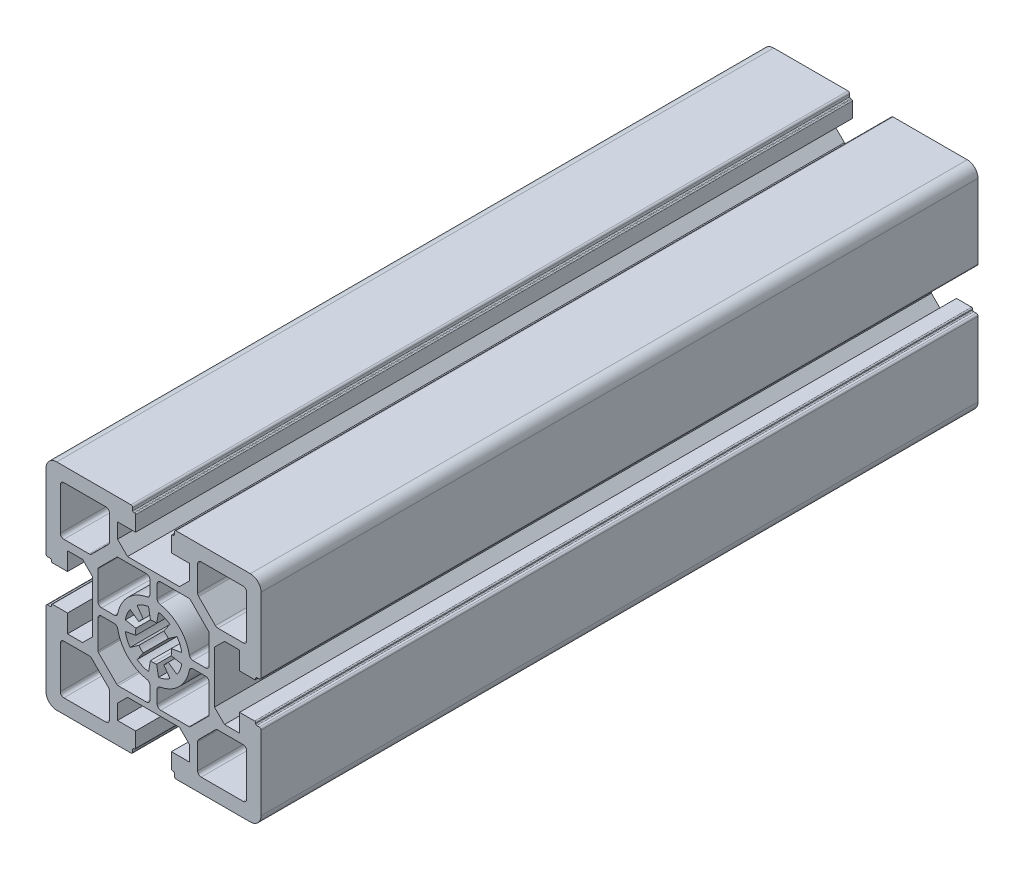
SolidWorks part; units mm, degrees
ref_plane "Front Plane" through (0, 0, 0) normal (0, 0, 1) x (1, 0, 0)
ref_plane "Top Plane" through (0, 0, 0) normal (0, 1, 0) x (1, 0, 0)
ref_plane "Right Plane" through (0, 0, 0) normal (1, 0, 0) x (0, 0, -1)
sketch "Sketch1" plane through (0, 0, 0) normal (0, 0, 1) x (1, 0, 0)
  line L0 (25, 12.3) -> (17.9642, 12.3)
  line L1 (17.2571, 12.5929) -> (12.5929, 17.2571)
  line L2 (12.3, 17.9642) -> (12.3, 25)
  line L3 (25, 26) -> (13.3, 26)
  line L4 (26, 13.3) -> (26, 25)
  line L5 (-0.8683, 4.924) -> (-1.3892, 7.8785)
  line L6 (-4.5886, 6.5532) -> (-2.8679, 4.0958)
  line L7 (-4.0958, 2.8679) -> (-6.5532, 4.5886)
  line L8 (-7.8785, 1.3892) -> (-4.9241, 0.8683)
  line L9 (14.5, 1) -> (10.9691, 1)
  line L10 (15.5, 2) -> (15.5, 9.9003)
  line L11 (15.3535, 10.2538) -> (10.2538, 15.3536)
  line L12 (9.9002, 15.5) -> (2, 15.5)
  line L13 (1, 10.9692) -> (1, 14.5)
  line L14 (7.25, 17) -> (0, 17)
  line L15 (10.05, 19.8) -> (7.25, 17)
  line L16 (10.05, 24) -> (10.05, 19.8)
  line L17 (5, 24) -> (10.05, 24)
  line L18 (5, 28.2) -> (5, 24)
  line L19 (5.5, 28.5) -> (5.3, 28.5)
  line L20 (5.8, 28.8) -> (5.8, 29.5)
  line L21 (27, 30) -> (6.3, 30)
  line L22 (30, 6.3) -> (30, 27)
  line L23 (29.5, 5.8) -> (28.8, 5.8)
  line L24 (28.5, 5.3) -> (28.5, 5.5)
  line L25 (24, 5) -> (28.2, 5)
  line L26 (24, 10.05) -> (24, 5)
  line L27 (19.8, 10.05) -> (24, 10.05)
  line L28 (17, 7.25) -> (19.8, 10.05)
  line L29 (17, 7.25) -> (17, 0)
  line L30 (7.8784, 1.3892) -> (4.924, 0.8683)
  line L31 (4.0957, 2.8679) -> (6.5532, 4.5886)
  line L32 (4.5886, 6.5532) -> (2.8679, 4.0958)
  line L33 (0.8682, 4.924) -> (1.3892, 7.8785)
  line L34 (-25, -12.3) -> (-17.9642, -12.3)
  line L35 (-17.2571, -12.5929) -> (-12.5929, -17.2571)
  line L36 (-12.3, -17.9642) -> (-12.3, -25)
  line L37 (-25, -26) -> (-13.3, -26)
  line L38 (-26, -13.3) -> (-26, -25)
  line L39 (-14.5, -1) -> (-10.9692, -1)
  line L40 (-15.5, -2) -> (-15.5, -9.9002)
  line L41 (-17, 7.25) -> (-17, 0)
  line L42 (-17, 7.25) -> (-19.8, 10.05)
  line L43 (-19.8, 10.05) -> (-24, 10.05)
  line L44 (-24, 10.05) -> (-24, 5)
  line L45 (-24, 5) -> (-28.2, 5)
  line L46 (-28.5, 5.3) -> (-28.5, 5.5)
  line L47 (-29.5, 5.8) -> (-28.8, 5.8)
  line L48 (-30, 6.3) -> (-30, 27)
  line L49 (-27, 30) -> (-6.3, 30)
  line L50 (-5.8, 28.8) -> (-5.8, 29.5)
  line L51 (-5.5, 28.5) -> (-5.3, 28.5)
  line L52 (-5, 28.2) -> (-5, 24)
  line L53 (-5, 24) -> (-10.05, 24)
  line L54 (-10.05, 24) -> (-10.05, 19.8)
  line L55 (-10.05, 19.8) -> (-7.25, 17)
  line L56 (-7.25, 17) -> (0, 17)
  line L57 (-15.3536, -10.2538) -> (-10.2538, -15.3535)
  line L58 (-9.9003, -15.5) -> (-2, -15.5)
  line L59 (-1, -10.9691) -> (-1, -14.5)
  line L60 (-7.25, -17) -> (0, -17)
  line L61 (-10.05, -19.8) -> (-7.25, -17)
  line L62 (-10.05, -24) -> (-10.05, -19.8)
  line L63 (-5, -24) -> (-10.05, -24)
  line L64 (-5, -28.2) -> (-5, -24)
  line L65 (-5.5, -28.5) -> (-5.3, -28.5)
  line L66 (-5.8, -28.8) -> (-5.8, -29.5)
  line L67 (-27, -30) -> (-6.3, -30)
  line L68 (-30, -6.3) -> (-30, -27)
  line L69 (-29.5, -5.8) -> (-28.8, -5.8)
  line L70 (-28.5, -5.3) -> (-28.5, -5.5)
  line L71 (-24, -5) -> (-28.2, -5)
  line L72 (-24, -10.05) -> (-24, -5)
  line L73 (-19.8, -10.05) -> (-24, -10.05)
  line L74 (-17, -7.25) -> (-19.8, -10.05)
  line L75 (-17, 0) -> (-17, -7.25)
  line L76 (0.8682, -4.924) -> (1.3892, -7.8784)
  line L77 (4.5886, -6.5532) -> (2.8679, -4.0957)
  line L78 (4.0957, -2.8679) -> (6.5532, -4.5886)
  line L79 (7.8784, -1.3892) -> (4.924, -0.8682)
  line L80 (17, 0) -> (17, -7.25)
  line L81 (17, -7.25) -> (19.8, -10.05)
  line L82 (19.8, -10.05) -> (24, -10.05)
  line L83 (24, -10.05) -> (24, -5)
  line L84 (24, -5) -> (28.2, -5)
  line L85 (28.5, -5.3) -> (28.5, -5.5)
  line L86 (29.5, -5.8) -> (28.8, -5.8)
  line L87 (30, -6.3) -> (30, -27)
  line L88 (27, -30) -> (6.3, -30)
  line L89 (5.8, -28.8) -> (5.8, -29.5)
  line L90 (5.5, -28.5) -> (5.3, -28.5)
  line L91 (5, -28.2) -> (5, -24)
  line L92 (5, -24) -> (10.05, -24)
  line L93 (10.05, -24) -> (10.05, -19.8)
  line L94 (10.05, -19.8) -> (7.25, -17)
  line L95 (7.25, -17) -> (0, -17)
  line L96 (1, -10.9691) -> (1, -14.5)
  line L97 (9.9002, -15.5) -> (2, -15.5)
  line L98 (15.3535, -10.2538) -> (10.2538, -15.3535)
  line L99 (15.5, -2) -> (15.5, -9.9002)
  line L100 (-1, 10.9692) -> (-1, 14.5)
  line L101 (-9.9003, 15.5) -> (-2, 15.5)
  line L102 (-15.3536, 10.2538) -> (-10.2538, 15.3536)
  line L103 (-15.5, 2) -> (-15.5, 9.9003)
  line L104 (-14.5, 1) -> (-10.9692, 1)
  line L105 (-26, 13.3) -> (-26, 25)
  line L106 (-25, 26) -> (-13.3, 26)
  line L107 (-12.3, 17.9642) -> (-12.3, 25)
  line L108 (-17.2571, 12.5929) -> (-12.5929, 17.2571)
  line L109 (-25, 12.3) -> (-17.9642, 12.3)
  line L110 (14.5, -1) -> (10.9691, -1)
  line L111 (-7.8785, -1.3892) -> (-4.9241, -0.8682)
  line L112 (-4.0958, -2.8679) -> (-6.5532, -4.5886)
  line L113 (-4.5886, -6.5532) -> (-2.8679, -4.0957)
  line L114 (-0.8683, -4.924) -> (-1.3892, -7.8784)
  line L115 (26, -13.3) -> (26, -25)
  line L116 (25, -26) -> (13.3, -26)
  line L117 (12.3, -17.9642) -> (12.3, -25)
  line L118 (17.2571, -12.5929) -> (12.5929, -17.2571)
  line L119 (25, -12.3) -> (17.9642, -12.3)
  line L120 (0, 0) -> (0, 50.387) construction
  line L121 (0, 0) -> (0, -41.9308) construction
  line L122 (0, 0) -> (51.9943, 0) construction
  line L123 (0, 0) -> (-54.8745, 0) construction
  arc A0 (17.9642, 12.3) -> (17.2571, 12.5929) centre (17.9642, 13.3) cw
  arc A1 (12.5929, 17.2571) -> (12.3, 17.9642) centre (13.3, 17.9642) cw
  arc A2 (12.3, 25) -> (13.3, 26) centre (13.3, 25) cw
  arc A3 (25, 26) -> (26, 25) centre (25, 25) cw
  arc A4 (26, 13.3) -> (25, 12.3) centre (25, 13.3) cw
  arc A5 (0, 5) -> (-0.8683, 4.924) centre (0, 0) ccw
  arc A6 (-1.3892, 7.8785) -> (-4.5886, 6.5532) centre (0, 0) ccw
  arc A7 (-2.8679, 4.0958) -> (-4.0958, 2.8679) centre (0, 0) ccw
  arc A8 (-6.5532, 4.5886) -> (-7.8785, 1.3892) centre (0, 0) ccw
  arc A9 (-4.9241, 0.8683) -> (-4.9241, -0.8682) centre (0, 0) ccw
  arc A10 (15.5, 2) -> (14.5, 1) centre (14.5, 2) cw
  arc A11 (15.3535, 10.2538) -> (15.5, 9.9003) centre (15, 9.9003) cw
  arc A12 (9.9002, 15.5) -> (10.2538, 15.3536) centre (9.9002, 15) cw
  arc A13 (1, 14.5) -> (2, 15.5) centre (2, 14.5) cw
  arc A14 (1.8206, 9.9854) -> (1, 10.9692) centre (2, 10.9692) cw
  arc A15 (1.8206, 9.9854) -> (9.9853, 1.8206) centre (0, 0) cw
  arc A16 (10.9691, 1) -> (9.9853, 1.8206) centre (10.9691, 2) cw
  arc A17 (5, 28.2) -> (5.3, 28.5) centre (5.3, 28.2) cw
  arc A18 (5.8, 28.8) -> (5.5, 28.5) centre (5.5, 28.8) cw
  arc A19 (5.8, 29.5) -> (6.3, 30) centre (6.3, 29.5) cw
  arc A20 (27, 30) -> (30, 27) centre (27, 27) cw
  arc A21 (30, 6.3) -> (29.5, 5.8) centre (29.5, 6.3) cw
  arc A22 (28.5, 5.5) -> (28.8, 5.8) centre (28.8, 5.5) cw
  arc A23 (28.5, 5.3) -> (28.2, 5) centre (28.2, 5.3) cw
  arc A24 (4.924, 0.8683) -> (4.924, -0.8682) centre (0, 0) cw
  arc A25 (6.5532, 4.5886) -> (7.8784, 1.3892) centre (0, 0) cw
  arc A26 (2.8679, 4.0958) -> (4.0957, 2.8679) centre (0, 0) cw
  arc A27 (1.3892, 7.8785) -> (4.5886, 6.5532) centre (0, 0) cw
  arc A28 (-28.5, 5.3) -> (-28.2, 5) centre (-28.2, 5.3) ccw
  arc A29 (-28.5, 5.5) -> (-28.8, 5.8) centre (-28.8, 5.5) ccw
  arc A30 (-30, 6.3) -> (-29.5, 5.8) centre (-29.5, 6.3) ccw
  arc A31 (-27, 30) -> (-30, 27) centre (-27, 27) ccw
  arc A32 (-5.8, 29.5) -> (-6.3, 30) centre (-6.3, 29.5) ccw
  arc A33 (-5.8, 28.8) -> (-5.5, 28.5) centre (-5.5, 28.8) ccw
  arc A34 (-5, 28.2) -> (-5.3, 28.5) centre (-5.3, 28.2) ccw
  arc A35 (0, 5) -> (0.8682, 4.924) centre (0, 0) cw
  arc A36 (-17.9642, -12.3) -> (-17.2571, -12.5929) centre (-17.9642, -13.3) cw
  arc A37 (-12.5929, -17.2571) -> (-12.3, -17.9642) centre (-13.3, -17.9642) cw
  arc A38 (-12.3, -25) -> (-13.3, -26) centre (-13.3, -25) cw
  arc A39 (-25, -26) -> (-26, -25) centre (-25, -25) cw
  arc A40 (-26, -13.3) -> (-25, -12.3) centre (-25, -13.3) cw
  arc A41 (-15.5, -2) -> (-14.5, -1) centre (-14.5, -2) cw
  arc A42 (-15.3536, -10.2538) -> (-15.5, -9.9002) centre (-15, -9.9002) cw
  arc A43 (-9.9003, -15.5) -> (-10.2538, -15.3535) centre (-9.9003, -15) cw
  arc A44 (-1, -14.5) -> (-2, -15.5) centre (-2, -14.5) cw
  arc A45 (-1.8206, -9.9853) -> (-1, -10.9691) centre (-2, -10.9691) cw
  arc A46 (-1.8206, -9.9853) -> (-9.9854, -1.8206) centre (0, 0) cw
  arc A47 (-10.9692, -1) -> (-9.9854, -1.8206) centre (-10.9692, -2) cw
  arc A48 (0, -4.9999) -> (0.8682, -4.924) centre (0, 0) ccw
  arc A49 (-5, -28.2) -> (-5.3, -28.5) centre (-5.3, -28.2) cw
  arc A50 (-5.8, -28.8) -> (-5.5, -28.5) centre (-5.5, -28.8) cw
  arc A51 (-5.8, -29.5) -> (-6.3, -30) centre (-6.3, -29.5) cw
  arc A52 (-27, -30) -> (-30, -27) centre (-27, -27) cw
  arc A53 (-30, -6.3) -> (-29.5, -5.8) centre (-29.5, -6.3) cw
  arc A54 (-28.5, -5.5) -> (-28.8, -5.8) centre (-28.8, -5.5) cw
  arc A55 (-28.5, -5.3) -> (-28.2, -5) centre (-28.2, -5.3) cw
  arc A56 (1.3892, -7.8784) -> (4.5886, -6.5532) centre (0, 0) ccw
  arc A57 (2.8679, -4.0957) -> (4.0957, -2.8679) centre (0, 0) ccw
  arc A58 (6.5532, -4.5886) -> (7.8784, -1.3892) centre (0, 0) ccw
  arc A59 (28.5, -5.3) -> (28.2, -5) centre (28.2, -5.3) ccw
  arc A60 (28.5, -5.5) -> (28.8, -5.8) centre (28.8, -5.5) ccw
  arc A61 (30, -6.3) -> (29.5, -5.8) centre (29.5, -6.3) ccw
  arc A62 (27, -30) -> (30, -27) centre (27, -27) ccw
  arc A63 (5.8, -29.5) -> (6.3, -30) centre (6.3, -29.5) ccw
  arc A64 (5.8, -28.8) -> (5.5, -28.5) centre (5.5, -28.8) ccw
  arc A65 (5, -28.2) -> (5.3, -28.5) centre (5.3, -28.2) ccw
  arc A66 (10.9691, -1) -> (9.9853, -1.8206) centre (10.9691, -2) ccw
  arc A67 (1.8206, -9.9853) -> (9.9853, -1.8206) centre (0, 0) ccw
  arc A68 (-10.9692, 1) -> (-9.9854, 1.8206) centre (-10.9692, 2) ccw
  arc A69 (-1.8206, 9.9854) -> (-9.9854, 1.8206) centre (0, 0) ccw
  arc A70 (-1.8206, 9.9854) -> (-1, 10.9692) centre (-2, 10.9692) ccw
  arc A71 (-1, 14.5) -> (-2, 15.5) centre (-2, 14.5) ccw
  arc A72 (-9.9003, 15.5) -> (-10.2538, 15.3536) centre (-9.9003, 15) ccw
  arc A73 (-15.3536, 10.2538) -> (-15.5, 9.9003) centre (-15, 9.9003) ccw
  arc A74 (-15.5, 2) -> (-14.5, 1) centre (-14.5, 2) ccw
  arc A75 (-26, 13.3) -> (-25, 12.3) centre (-25, 13.3) ccw
  arc A76 (-25, 26) -> (-26, 25) centre (-25, 25) ccw
  arc A77 (-12.3, 25) -> (-13.3, 26) centre (-13.3, 25) ccw
  arc A78 (-12.5929, 17.2571) -> (-12.3, 17.9642) centre (-13.3, 17.9642) ccw
  arc A79 (-17.9642, 12.3) -> (-17.2571, 12.5929) centre (-17.9642, 13.3) ccw
  arc A80 (1.8206, -9.9853) -> (1, -10.9691) centre (2, -10.9691) ccw
  arc A81 (1, -14.5) -> (2, -15.5) centre (2, -14.5) ccw
  arc A82 (9.9002, -15.5) -> (10.2538, -15.3535) centre (9.9002, -15) ccw
  arc A83 (15.3535, -10.2538) -> (15.5, -9.9002) centre (15, -9.9002) ccw
  arc A84 (15.5, -2) -> (14.5, -1) centre (14.5, -2) ccw
  arc A85 (-6.5532, -4.5886) -> (-7.8785, -1.3892) centre (0, 0) cw
  arc A86 (-2.8679, -4.0957) -> (-4.0958, -2.8679) centre (0, 0) cw
  arc A87 (-1.3892, -7.8784) -> (-4.5886, -6.5532) centre (0, 0) cw
  arc A88 (0, -4.9999) -> (-0.8683, -4.924) centre (0, 0) cw
  arc A89 (26, -13.3) -> (25, -12.3) centre (25, -13.3) ccw
  arc A90 (25, -26) -> (26, -25) centre (25, -25) ccw
  arc A91 (12.3, -25) -> (13.3, -26) centre (13.3, -25) ccw
  arc A92 (12.5929, -17.2571) -> (12.3, -17.9642) centre (13.3, -17.9642) ccw
  arc A93 (17.9642, -12.3) -> (17.2571, -12.5929) centre (17.9642, -13.3) ccw
  dimension "D6" = 13
  dimension "D4" = 10
  dimension "D1" = 60
  dimension "D2" = 60
  dimension "D3" = 30
  dimension "D5" = 10
extrude "Base-Extrude" add sketch "Sketch1" against normal blind 200
